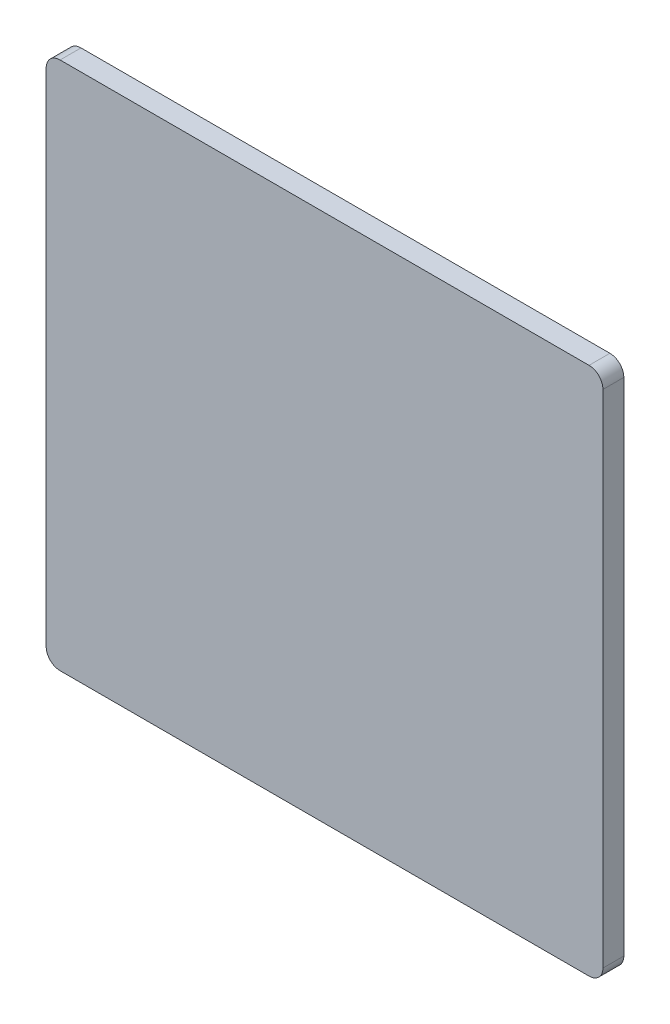
SolidWorks part; units mm, degrees
ref_plane "Front" through (0, 0, 0) normal (0, 0, 1) x (1, 0, 0)
ref_plane "Top" through (0, 0, 0) normal (0, 1, 0) x (1, 0, 0)
ref_plane "Right" through (0, 0, 0) normal (1, 0, 0) x (0, 0, -1)
sketch "Sketch1" plane through (0, 0, 0) normal (0, 0, 1) x (1, 0, 0)
  line L1 (-127, -120.65) -> (127, -120.65)
  line L2 (-127, -120.65) -> (-127, 120.65)
  line L3 (-127, 120.65) -> (127, 120.65)
  line L4 (127, -120.65) -> (127, 120.65)
  line L5 (-127, -120.65) -> (127, 120.65) construction
  line L6 (-127, 120.65) -> (127, -120.65) construction
  point P0 (0, 0)
  dimension "D1" = 254
  dimension "D2" = 241.3
extrude "Boss-Extrude1" add sketch "Sketch1" along normal blind 9.525
fillet "Fillet1" radius 6.35 4 edges at (-127, -120.65, 4.7625) (127, -120.65, 4.7625) (127, 120.65, 4.7625) (-127, 120.65, 4.7625)
